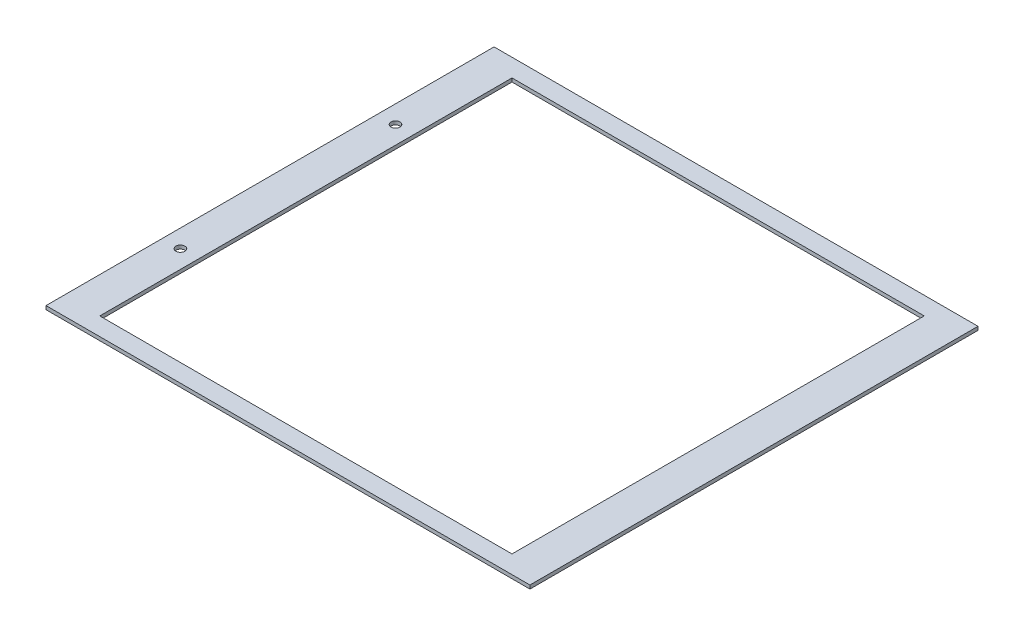
SolidWorks part; units mm, degrees
ref_plane "Спереди" through (0, 0, 0) normal (0, 0, 1) x (1, 0, 0)
ref_plane "Сверху" through (0, 0, 0) normal (0, 1, 0) x (1, 0, 0)
ref_plane "Справа" through (0, 0, 0) normal (1, 0, 0) x (0, 0, -1)
sketch "Эскиз1" plane through (0, 0, 0) normal (0, 1, 0) x (1, 0, 0)
  line L0 (145.9149, 135) -> (145.9149, 115) construction
  line L1 (-115, 115) -> (115, 115)
  line L2 (-115, 115) -> (-115, -115)
  line L3 (-115, -115) -> (115, -115)
  line L4 (115, 115) -> (115, -115)
  line L5 (-115, 115) -> (115, -115) construction
  line L6 (-115, -115) -> (115, 115) construction
  line L8 (-135, -125) -> (-135, 125)
  line L9 (145.9149, -135) -> (145.9149, -115) construction
  line L10 (135, -125) -> (135, 125)
  line L11 (-125, -125) -> (125, 125) construction
  line L12 (-125, 125) -> (125, -125) construction
  line L13 (135, 125) -> (-135, 125)
  line L14 (135, -125) -> (-135, -125)
  point P0 (0, 0)
  point P5 (0, 0)
  dimension "D1" = 230
extrude "Бобышка-Вытянуть1" add sketch "Эскиз1" along normal blind 2
sketch "Эскиз2" plane through (0, 2, 0) normal (0, 1, 0) x (1, 0, 0)
  line L0 (-149.3805, 0) -> (-149.3805, 60) construction
  line L1 (-149.3805, 0) -> (-149.3805, -60) construction
  line L2 (-135, 142.2685) -> (-115, 142.2685) construction
  circle A0 centre (-125, 60) radius 2.5
  circle A1 centre (-125, -60) radius 2.5
  dimension "D1" = 60
  dimension "D2" = 60
  dimension "D3" = 5
  dimension "D4" = 5
extrude "Вырез-Вытянуть1" cut sketch "Эскиз2" against normal through all
